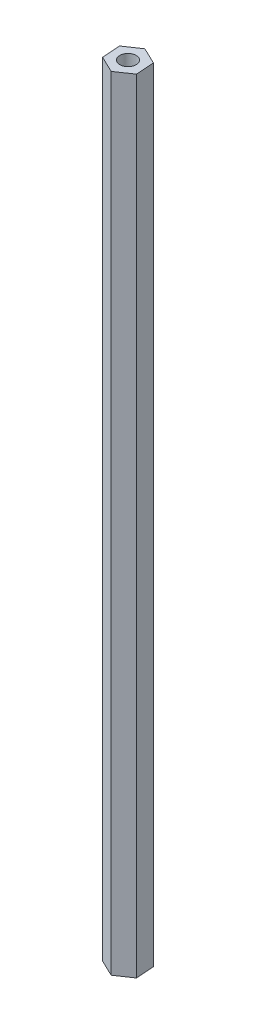
SolidWorks part; units mm, degrees
ref_plane "Front Plane" through (0, 0, 0) normal (0, 0, 1) x (1, 0, 0)
ref_plane "Top Plane" through (0, 0, 0) normal (0, 1, 0) x (1, 0, 0)
ref_plane "Right Plane" through (0, 0, 0) normal (1, 0, 0) x (0, 0, -1)
sketch "Sketch1" plane through (0, 0, 0) normal (0, 1, 0) x (1, 0, 0)
  line L1 (6.0569, 4.1325) -> (-0.5505, 7.3117)
  line L2 (-0.5505, 7.3117) -> (-6.6073, 3.1791)
  line L3 (-6.6073, 3.1791) -> (-6.0569, -4.1325)
  line L4 (-6.0569, -4.1325) -> (0.5505, -7.3117)
  line L5 (0.5505, -7.3117) -> (6.6073, -3.1791)
  line L6 (6.6073, -3.1791) -> (6.0569, 4.1325)
  circle A0 centre (0, 0) radius 6.35 construction
  dimension "D1" = 12.7
extrude "Boss-Extrude1" add sketch "Sketch1" along normal mid plane 314.198
sketch "Sketch2" plane through (0, 157.099, 0) normal (0, 1, 0) x (1, 0, 0)
  circle A0 centre (0, 0) radius 3.2639
  dimension "D1" = 6.5278
extrude "Cut-Extrude1" cut sketch "Sketch2" against normal blind 12.7
mirror "Mirror1" about plane through (0, 0, 0) normal (0, 1, 0) of "Cut-Extrude1"
